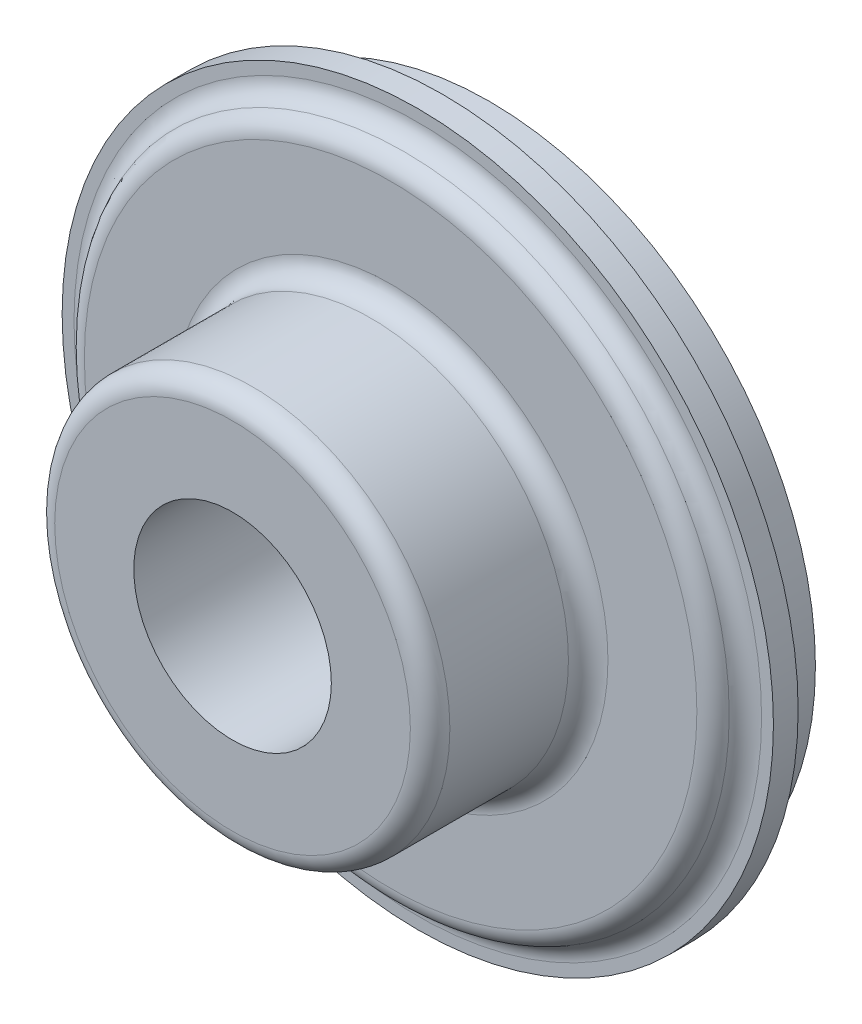
SolidWorks part; units mm, degrees
ref_plane "Front Plane" through (0, 0, 0) normal (0, 0, 1) x (1, 0, 0)
ref_plane "Top Plane" through (0, 0, 0) normal (0, 1, 0) x (1, 0, 0)
ref_plane "Right Plane" through (0, 0, 0) normal (1, 0, 0) x (0, 0, -1)
sketch "Sketch1" plane through (0, 0, 0) normal (0, 1, 0) x (1, 0, 0)
  line L0 (22, -227) -> (31, -227)
  line L1 (34.7997, -224.25) -> (36, -224.25)
  line L2 (36, -224.25) -> (36, -221.75)
  line L3 (36, -221.75) -> (33, -221.75)
  line L4 (33, -221.75) -> (33, -217)
  line L5 (33, -217) -> (27, -217)
  line L6 (27, -217) -> (27, -223)
  line L7 (27, -223) -> (21.8199, -223)
  line L8 (21.8199, -223) -> (20, -218)
  line L9 (20, -218) -> (20, -213)
  line L10 (20, -213) -> (18.6591, -209.316)
  line L11 (16.7797, -208) -> (12, -208)
  line L12 (10, -210) -> (10, -243)
  line L13 (10, -243) -> (18, -243)
  line L14 (20, -241) -> (20, -229)
  line L15 (0, -208) -> (0, -243) construction
  arc A0 (31, -227) -> (32.8998, -225.625) centre (31, -225) ccw
  arc A1 (32.8998, -225.625) -> (34.7997, -224.25) centre (34.7997, -226.25) cw
  arc A2 (18.6591, -209.316) -> (16.7797, -208) centre (16.7797, -210) ccw
  arc A3 (12, -208) -> (10, -210) centre (12, -210) ccw
  arc A4 (18, -243) -> (20, -241) centre (18, -241) ccw
  arc A5 (20, -229) -> (22, -227) centre (22, -229) cw
revolve "Revolve1" add sketch "Sketch1" angle 360 about L15
